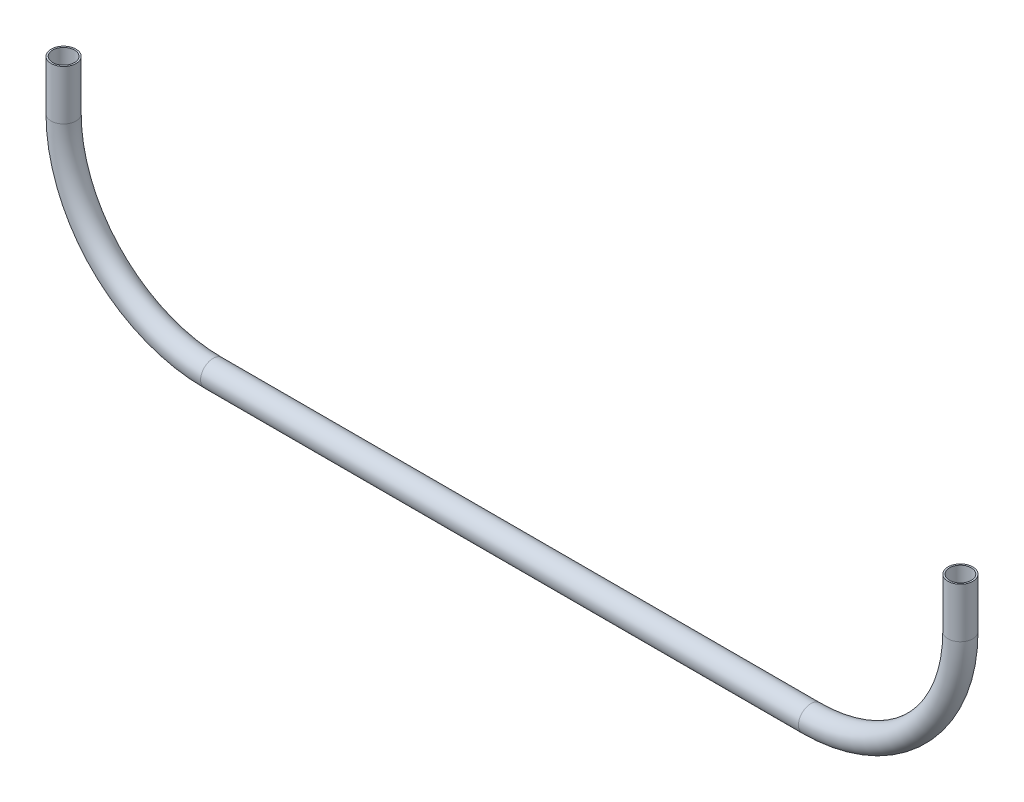
SolidWorks part; units mm, degrees
ref_plane "Front Plane" through (0, 0, 0) normal (0, 0, 1) x (1, 0, 0)
ref_plane "Top Plane" through (0, 0, 0) normal (0, 1, 0) x (1, 0, 0)
ref_plane "Right Plane" through (0, 0, 0) normal (1, 0, 0) x (0, 0, -1)
sketch "Sketch1" plane through (0, 0, 0) normal (0, 0, 1) x (1, 0, 0)
  line L0 (-152.4, 0) -> (152.4, 0)
  line L1 (-228.6, 76.2) -> (-228.6, 101.6)
  line L3 (228.6, 76.2) -> (228.6, 101.6)
  arc A0 (152.4, 0) -> (228.6, 76.2) centre (152.4, 76.2) ccw
  arc A1 (-152.4, 0) -> (-228.6, 76.2) centre (-152.4, 76.2) cw
  point P3 (0, 0)
  point P8 (228.6, 0)
  point P11 (-228.6, 0)
  dimension "D3" = 76.2
  dimension "D1" = 457.2
  dimension "D2" = 101.6
ref_plane "Plane1" through (-228.6, 101.6, 0) normal (0, 1, 0) x (1, 0, 0)
sketch "Sketch2" plane through (-228.6, 101.6, 0) normal (0, 1, 0) x (1, 0, 0)
  circle A0 centre (0, 0) radius 6.35
  circle A1 centre (0, 0) radius 5.5562
  dimension "D1" = 0.7937
  dimension "D2" = 12.7
sweep "Sweep1" add profiles "Sketch2" path "Sketch1"
